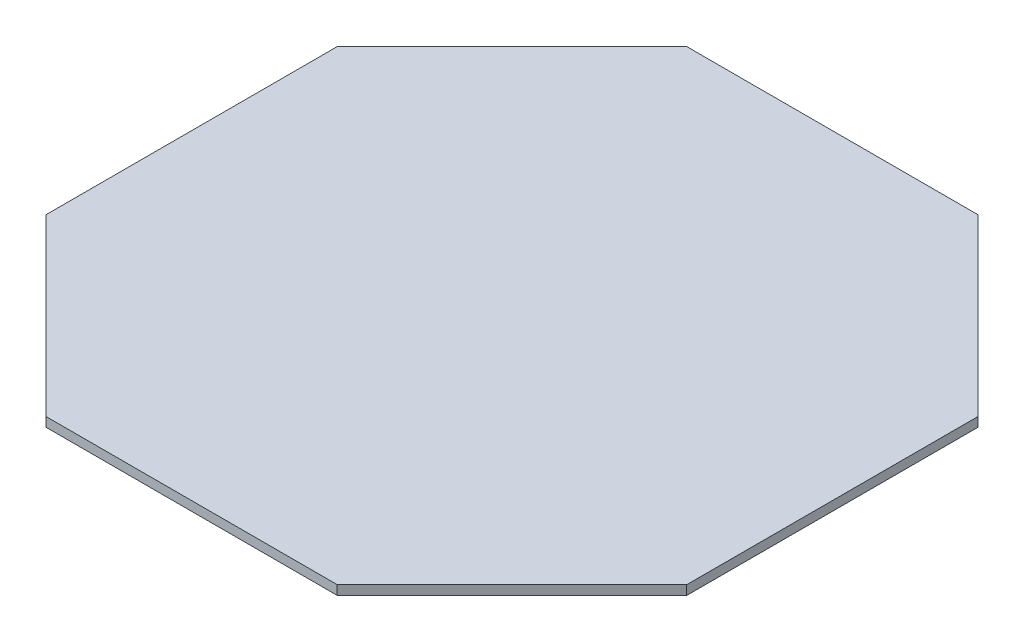
SolidWorks part; units mm, degrees
ref_plane "Front Plane" through (0, 0, 0) normal (0, 0, 1) x (1, 0, 0)
ref_plane "Top Plane" through (0, 0, 0) normal (0, 1, 0) x (1, 0, 0)
ref_plane "Right Plane" through (0, 0, 0) normal (1, 0, 0) x (0, 0, -1)
sketch "Sketch1" plane through (0, 0, 0) normal (0, 1, 0) x (1, 0, 0)
  line L0 (-55, 25) -> (-55, -25)
  line L1 (-55, -25) -> (-25, -55)
  line L2 (-25, -55) -> (25, -55)
  line L3 (25, -55) -> (55, -25)
  line L4 (55, -25) -> (55, 25)
  line L5 (55, 25) -> (25, 55)
  line L6 (25, 55) -> (-25, 55)
  line L7 (-25, 55) -> (-55, 25)
  point P7 (0, 55)
  point P9 (-55, 0)
  point P10 (0, 0)
  point P12 (0, 0)
  dimension "D1" = 50
  dimension "D2" = 30
  dimension "D3" = 30
  dimension "D4" = 30
extrude "Boss-Extrude1" add sketch "Sketch1" along normal mid plane 1.6
equation "\"D4@Sketch1\"=\"D2@Sketch1\""
equation "\"D3@Sketch1\"=\"D2@Sketch1\""
